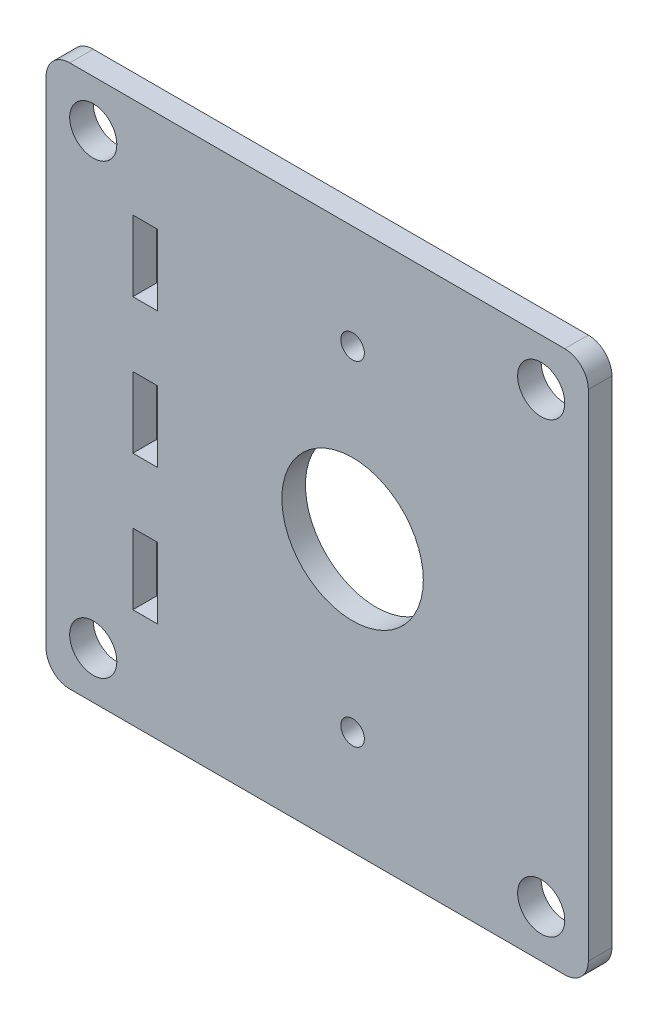
SolidWorks part; units mm, degrees
ref_plane "Front Plane" through (0, 0, 0) normal (0, 0, 1) x (1, 0, 0)
ref_plane "Top Plane" through (0, 0, 0) normal (0, 1, 0) x (1, 0, 0)
ref_plane "Right Plane" through (0, 0, 0) normal (1, 0, 0) x (0, 0, -1)
sketch "Sketch1" plane through (0, 0, 0) normal (0, 0, 1) x (1, 0, 0)
  line L0 (0, 73.025) -> (0, -73.025) construction
  line L1 (63.5, 73.025) -> (-82.55, 73.025)
  line L2 (63.5, 73.025) -> (63.5, -73.025)
  line L3 (63.5, -73.025) -> (-82.55, -73.025)
  line L4 (-82.55, 73.025) -> (-82.55, -73.025)
  line L5 (0, 45) -> (0, -45) construction
  line L6 (-55.88, 73.025) -> (-55.88, 36.5125) construction
  line L7 (-59.182, -9.525) -> (-52.578, -9.525)
  line L8 (-59.182, -9.525) -> (-59.182, 9.525)
  line L9 (-59.182, 9.525) -> (-52.578, 9.525)
  line L10 (-52.578, -9.525) -> (-52.578, 9.525)
  line L11 (-59.182, -9.525) -> (-52.578, 9.525) construction
  line L12 (-59.182, 9.525) -> (-52.578, -9.525) construction
  line L13 (-59.182, 46.0375) -> (-52.578, 46.0375)
  line L14 (-59.182, 46.0375) -> (-59.182, 26.9875)
  line L15 (-59.182, 26.9875) -> (-52.578, 26.9875)
  line L16 (-52.578, 46.0375) -> (-52.578, 26.9875)
  line L17 (-59.182, 46.0375) -> (-52.578, 26.9875) construction
  line L18 (-59.182, 26.9875) -> (-52.578, 46.0375) construction
  line L19 (-59.182, -26.9875) -> (-52.578, -26.9875)
  line L20 (-59.182, -26.9875) -> (-59.182, -46.0375)
  line L21 (-59.182, -46.0375) -> (-52.578, -46.0375)
  line L22 (-52.578, -26.9875) -> (-52.578, -46.0375)
  line L23 (-59.182, -26.9875) -> (-52.578, -46.0375) construction
  line L24 (-59.182, -46.0375) -> (-52.578, -26.9875) construction
  line L25 (-55.88, 36.5125) -> (-55.88, 0) construction
  line L26 (-55.88, 0) -> (-55.88, -36.5125) construction
  line L27 (-55.88, -36.5125) -> (-55.88, -73.025) construction
  circle A0 centre (50.8, 60.325) radius 6.35
  circle A1 centre (50.8, -60.325) radius 6.35
  circle A2 centre (0, 0) radius 19.05
  circle A3 centre (0, 45) radius 3.175
  circle A4 centre (0, -45) radius 3.175
  circle A5 centre (-69.85, 60.325) radius 6.35
  circle A6 centre (-69.85, -60.325) radius 6.35
  point P0 (0, 0)
  point P14 (0, 0)
  point P19 (0, 0)
  point P24 (-55.88, 36.5125)
  point P28 (-55.88, 0)
  point P34 (-55.88, -36.5125)
  dimension "D2" = 12.7
  dimension "D6" = 38.1
  dimension "D8" = 6.35
  dimension "D1" = 146.05
  dimension "D3" = 12.7
  dimension "D4" = 12.7
  dimension "D5" = 50.8
  dimension "D7" = 90
  dimension "D9" = 12.7
  dimension "D10" = 82.55
  dimension "D11" = 12.7
  dimension "D12" = 19.05
  dimension "D13" = 6.604
  dimension "D14" = 55.88
extrude "Boss-Extrude1" add sketch "Sketch1" along normal mid plane 6.35
fillet "Fillet1" radius 6.35 4 edges at (63.5, -73.025, 0) (-82.55, -73.025, 0) (-82.55, 73.025, 0) (63.5, 73.025, 0)
